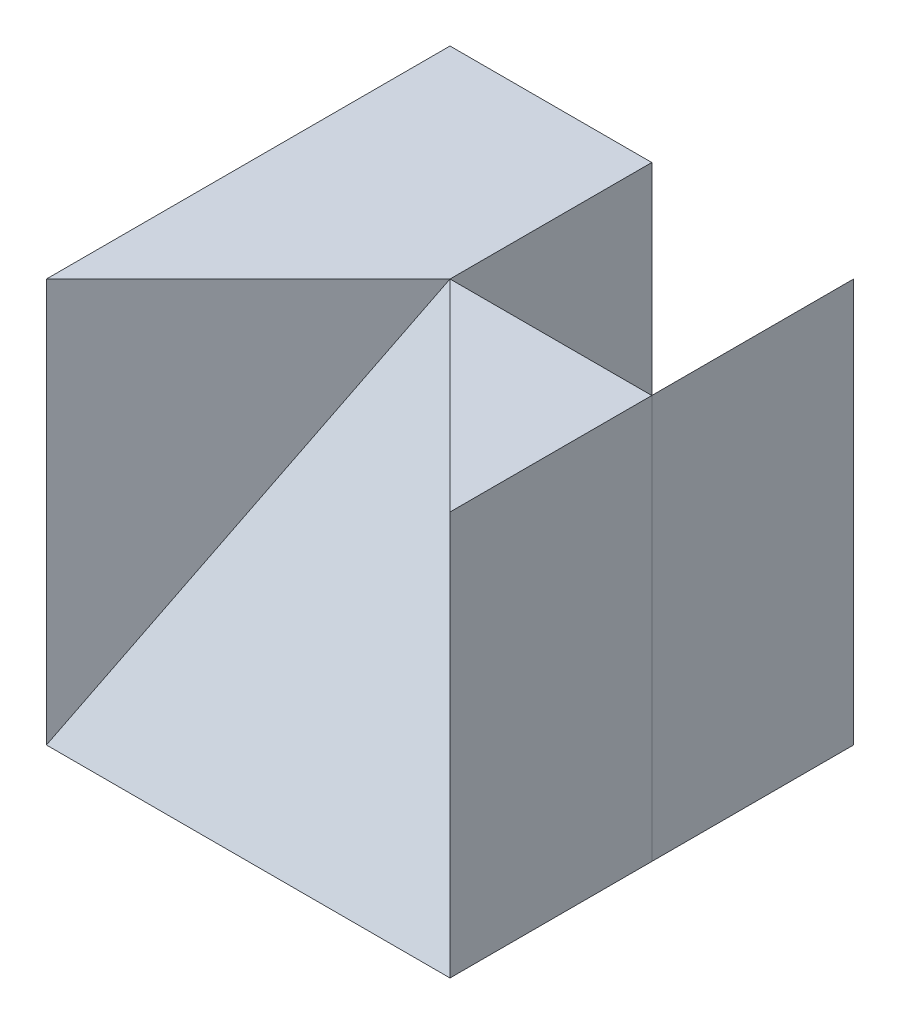
SolidWorks part; units mm, degrees
ref_plane "Front" through (0, 0, 0) normal (0, 0, 1) x (1, 0, 0)
ref_plane "Top" through (0, 0, 0) normal (0, 1, 0) x (1, 0, 0)
ref_plane "Right" through (0, 0, 0) normal (1, 0, 0) x (0, 0, -1)
sketch "Sketch2" plane through (0, 0, 0) normal (0, 1, 0) x (1, 0, 0)
  line L1 (-2, -2) -> (2, -2)
  line L2 (-2, -2) -> (-2, 2)
  line L3 (-2, 2) -> (2, 2)
  line L4 (2, -2) -> (2, 2)
  line L5 (-2, -2) -> (2, 2) construction
  line L6 (-2, 2) -> (2, -2) construction
  point P0 (0, 0)
  dimension "D1" = 4
  dimension "D2" = 4
extrude "Boss-Extrude1" add sketch "Sketch2" along normal blind 4
sketch3d "3DSketch1"
  line L0 (2, 4, -2) -> (-2, 4, -2) construction
  line L1 (-2, 4, -2) -> (-2, 4, 2) construction
  line L2 (-2, 0, 2) -> (0, 4, 0)
  line L3 (0, 4, 0) -> (2, 0, 2)
  line L4 (2, 0, 2) -> (-2, 0, 2)
  point P0 (0, 4, 0)
  dimension "D1" = 2
  dimension "D2" = 2
extrude "Cut-Extrude1" cut sketch "3DSketch1" along direction (0, -1, 0) on the side against the normal blind 10
sketch "Sketch5" plane through (0, 4, 0) normal (0, 1, 0) x (1, 0, 0)
  line L1 (0, 0) -> (2, 0)
  line L2 (0, 0) -> (0, 2)
  line L3 (0, 2) -> (2, 2)
  line L4 (2, 0) -> (2, 2)
extrude "Cut-Extrude5" cut sketch "Sketch5" against normal blind 10
sketch "Sketch6" plane through (0, 0, 0) normal (0, 0, -1) x (-1, 0, 0)
  line L0 (-2, 4) -> (0, 0)
  line L1 (0, 0) -> (-2, 0)
  line L2 (-2, 0) -> (-2, 4)
  point P7 (-2, 4.0087)
extrude "Boss-Extrude4" add sketch "Sketch6" along normal blind 2 separate body
